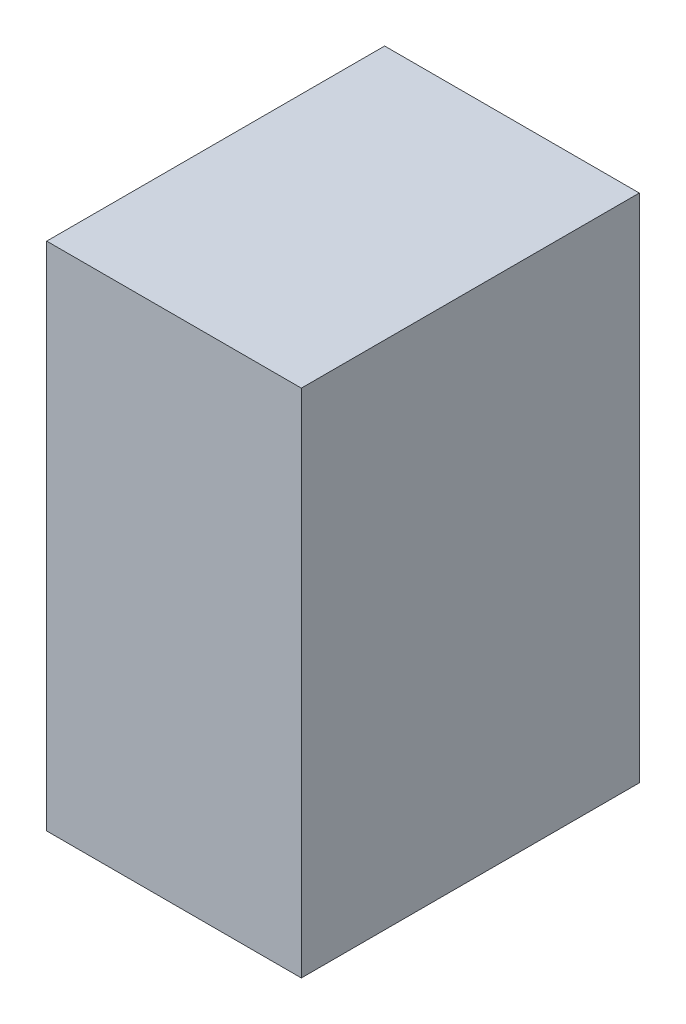
SolidWorks part; units mm, degrees
ref_plane "Front Plane" through (0, 0, 0) normal (0, 0, 1) x (1, 0, 0)
ref_plane "Top Plane" through (0, 0, 0) normal (0, 1, 0) x (1, 0, 0)
ref_plane "Right Plane" through (0, 0, 0) normal (1, 0, 0) x (0, 0, -1)
sketch "Sketch1" plane through (0, 0, 0) normal (0, 0, 1) x (1, 0, 0)
  line L1 (0, 0) -> (20.574, 0)
  line L2 (0, 0) -> (0, 41.275)
  line L3 (0, 41.275) -> (20.574, 41.275)
  line L4 (20.574, 0) -> (20.574, 41.275)
  dimension "D1" = 41.275
  dimension "D2" = 20.574
extrude "Boss-Extrude1" add sketch "Sketch1" along normal blind 27.305
